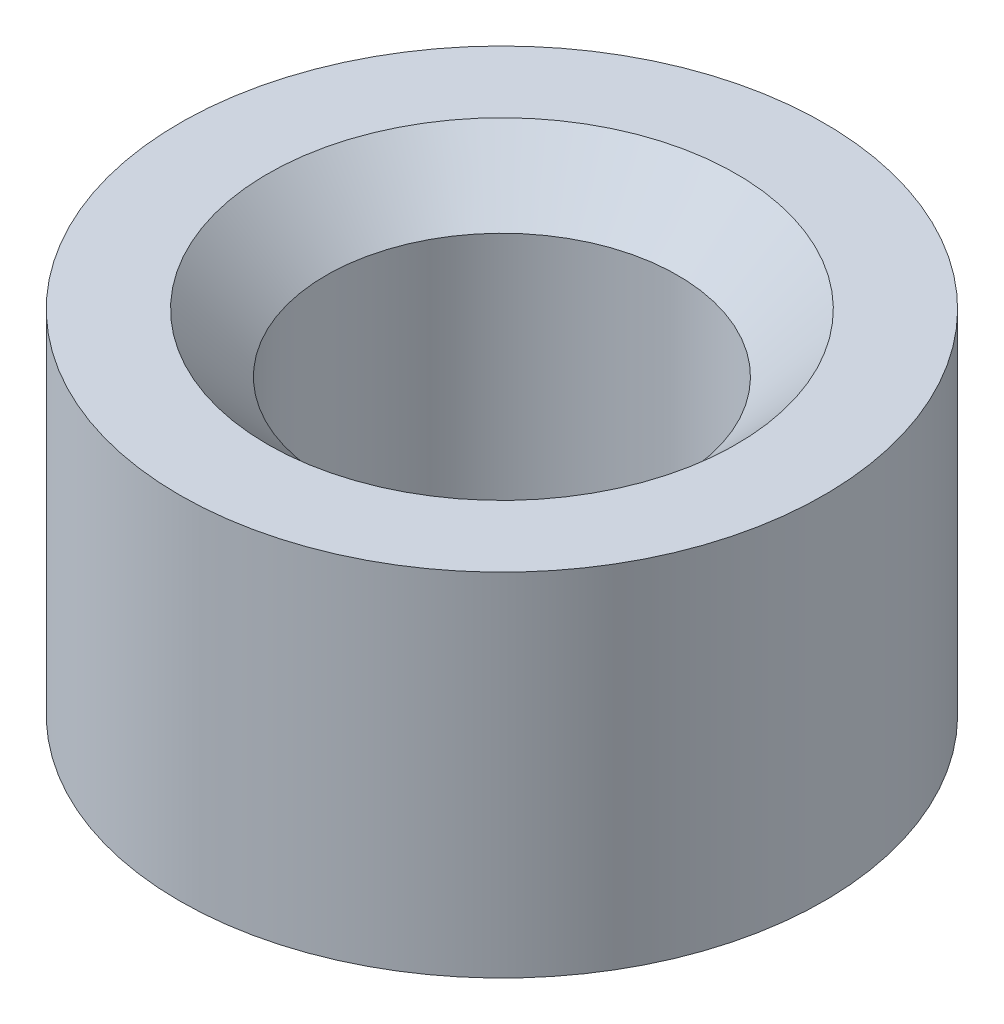
SolidWorks part; units mm, degrees
material "1060 Alloy"
ref_plane "Front Plane" through (0, 0, 0) normal (0, 0, 1) x (1, 0, 0)
ref_plane "Top Plane" through (0, 0, 0) normal (0, 1, 0) x (1, 0, 0)
ref_plane "Right Plane" through (0, 0, 0) normal (1, 0, 0) x (0, 0, -1)
sketch "Sketch1" plane through (0, 0, 0) normal (0, 1, 0) x (1, 0, 0)
  circle A0 centre (0, 0) radius 2.75
  circle A1 centre (0, 0) radius 1.5
  dimension "D1" = 5.5
  dimension "D2" = 3
extrude "Boss-Extrude1" add sketch "Sketch1" along normal blind 3
chamfer "Chamfer1" distance 0.5 angle 45 2 edges at (0, 3, 1.5) (0, 0, 1.5)
